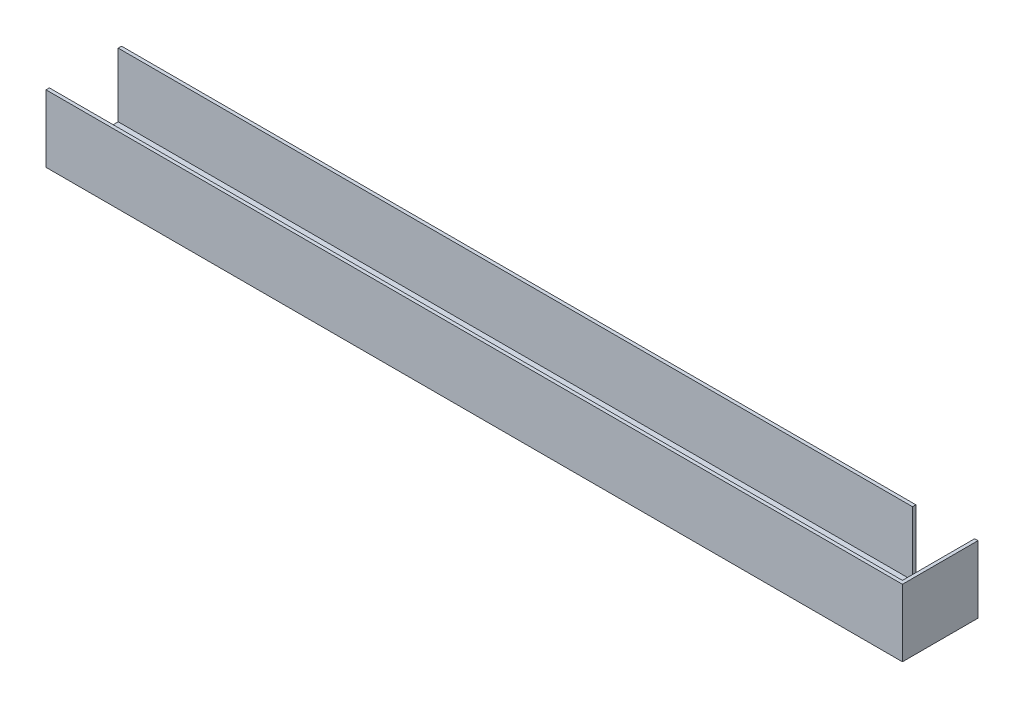
SolidWorks part; units mm, degrees
ref_plane "Front Plane" through (0, 0, 0) normal (0, 0, 1) x (1, 0, 0)
ref_plane "Top Plane" through (0, 0, 0) normal (0, 1, 0) x (1, 0, 0)
ref_plane "Right Plane" through (0, 0, 0) normal (1, 0, 0) x (0, 0, -1)
sketch "Sketch1" plane through (0, 0, 0) normal (0, 0, 1) x (1, 0, 0)
  line L0 (-647.7, 0) -> (647.7, 0)
  line L1 (-647.7, 0) -> (-647.7, 101.6)
  line L2 (-647.7, 101.6) -> (647.7, 101.6)
  line L3 (647.7, 101.6) -> (647.7, 0)
  point P4 (0, 0)
  dimension "D1" = 1295.4
  dimension "D2" = 101.6
extrude "Boss-Extrude1" add sketch "Sketch1" against normal blind 114.3
shell "Shell1" thickness 5.08
sketch "Sketch3" plane through (0, 0, -114.3) normal (0, 0, -1) x (-1, 0, 0)
  line L0 (-647.7, 101.6) -> (647.7, 101.6) construction
  line L1 (-642.62, 5.08) -> (-553.72, 5.08)
  line L2 (-642.62, 5.08) -> (-642.62, 101.6)
  line L3 (-642.62, 101.6) -> (-553.72, 101.6)
  line L4 (-553.72, 5.08) -> (-553.72, 101.6)
  dimension "D1" = 88.9
  dimension "D2" = 96.52
extrude "Cut-Extrude1" cut sketch "Sketch3" against normal up to surface (5.08 mm away) up to face at (-2.54, 53.34, -109.22)
